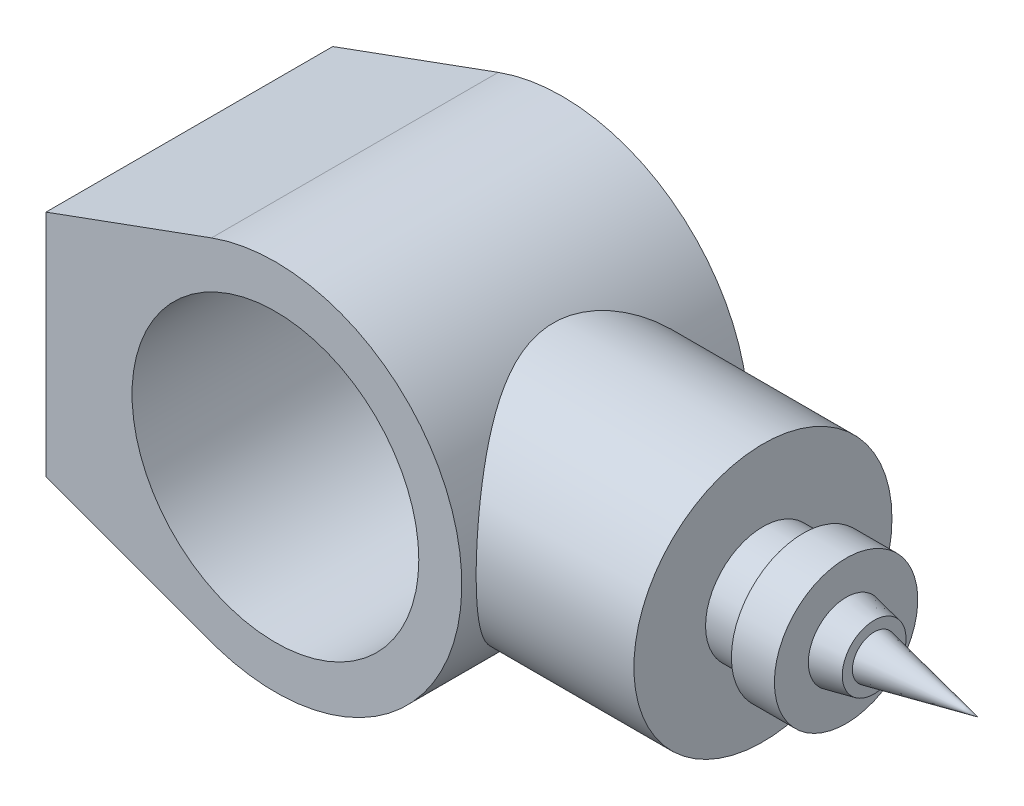
SolidWorks part; units mm, degrees
ref_plane "Front Plane" through (0, 0, 0) normal (0, 0, 1) x (1, 0, 0)
ref_plane "Top Plane" through (0, 0, 0) normal (0, 1, 0) x (1, 0, 0)
ref_plane "Right Plane" through (0, 0, 0) normal (1, 0, 0) x (0, 0, -1)
sketch "Sketch1" plane through (0, 0, 0) normal (0, 0, 1) x (1, 0, 0)
  line L0 (-80, -40) -> (-80, 40)
  line L1 (-80, 40) -> (-22.2817, 61.0617)
  line L2 (-80, -40) -> (-20.5102, -61.6793)
  arc A0 (-20.5102, -61.6793) -> (-22.2817, 61.0617) centre (0, 0) ccw
  circle A1 centre (0, 0) radius 50
  point P8 (-80, 0)
  dimension "D1" = 130
  dimension "D2" = 100
  dimension "D3" = 80
  dimension "D4" = 80
extrude "Boss-Extrude1" add sketch "Sketch1" along normal mid plane 100
ref_plane "Plane1" through (120, 0, 0) normal (1, 0, 0) x (0, 0, -1)
sketch "Sketch2" plane through (120, 0, 0) normal (1, 0, 0) x (0, 0, -1)
  circle A0 centre (0, 0) radius 45
  dimension "D1" = 90
extrude "Boss-Extrude2" add sketch "Sketch2" against normal up to next separate body
sketch "Sketch3" plane through (0, 0, 0) normal (0, 0, 1) x (1, 0, 0)
  line L0 (0, 0) -> (259.785, 0) construction
  line L1 (120, 0) -> (120, -20)
  line L2 (120, -45) -> (120, 45) construction
  line L3 (120, -20) -> (134, -20)
  line L4 (134, -20) -> (134, -25)
  line L5 (134, -25) -> (149, -25)
  line L6 (149, -25) -> (149, -13.1714)
  line L10 (195, 0) -> (120, 0)
  line L13 (149, -13.1714) -> (158.7872, -11.1195)
  line L14 (158.7872, -11.1195) -> (158.7872, -7.5918)
  line L15 (158.7872, -7.5918) -> (195, 0)
  dimension "D1" = 20
  dimension "D2" = 14
  dimension "D3" = 5
  dimension "D4" = 15
  dimension "D5" = 10
  dimension "D6" = 75
  dimension "D7" = 37
revolve "Revolve1" add sketch "Sketch3" angle 360 about L0
